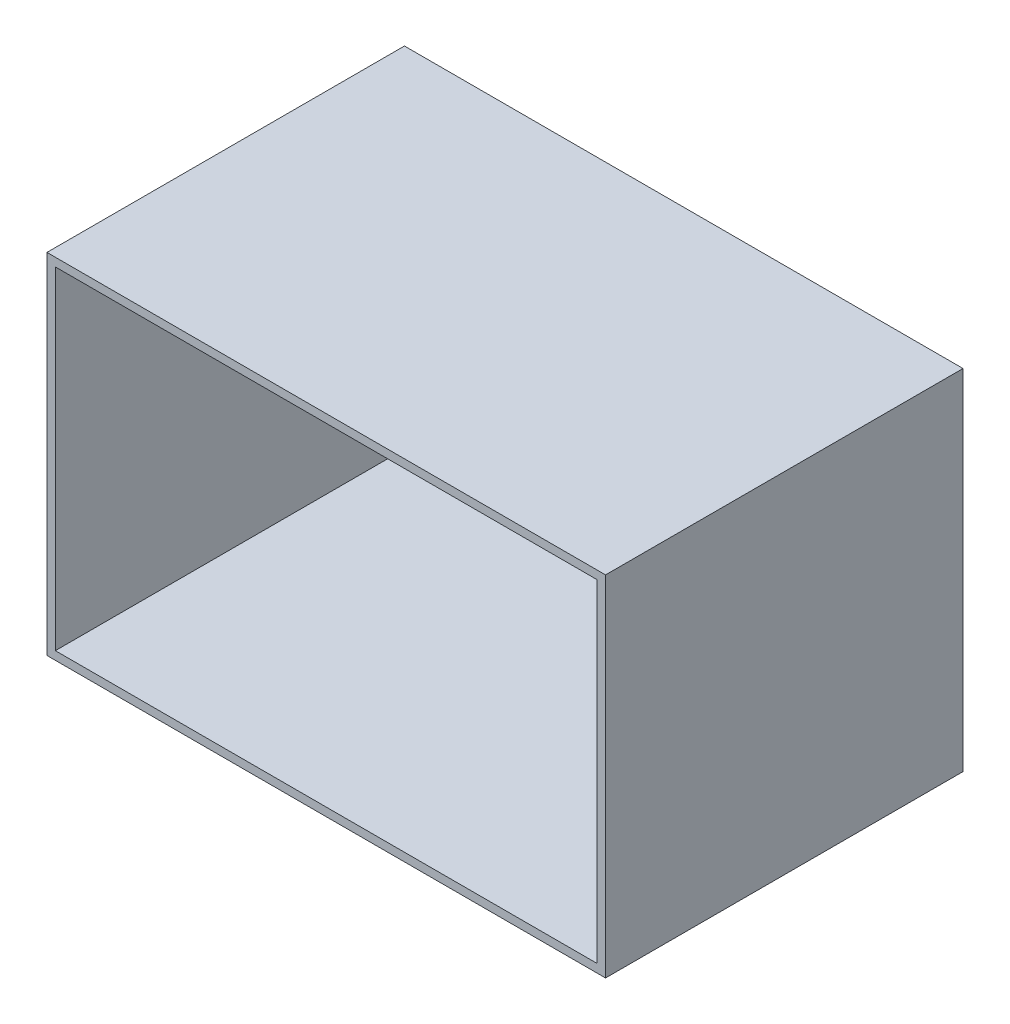
SolidWorks part; units mm, degrees
ref_plane "Alzado" through (0, 0, 0) normal (0, 0, 1) x (1, 0, 0)
ref_plane "Planta" through (0, 0, 0) normal (0, 1, 0) x (1, 0, 0)
ref_plane "Vista lateral" through (0, 0, 0) normal (1, 0, 0) x (0, 0, -1)
sketch "Croquis1" plane through (0, 0, 0) normal (0, 0, 1) x (1, 0, 0)
  line L1 (-200, 125) -> (200, 125)
  line L2 (-200, 125) -> (-200, -125)
  line L3 (-200, -125) -> (200, -125)
  line L4 (200, 125) -> (200, -125)
  line L5 (-200, 125) -> (200, -125) construction
  line L6 (-200, -125) -> (200, 125) construction
  point P0 (0, 0)
  dimension "D1" = 400
  dimension "D2" = 250
extrude "Saliente-Extruir2" add sketch "Croquis1" along normal blind 6
sketch "Croquis2" plane through (0, 0, 6) normal (0, 0, 1) x (1, 0, 0)
  line L1 (-194, 119) -> (194, 119)
  line L2 (-194, 119) -> (-194, -119)
  line L3 (-194, -119) -> (194, -119)
  line L4 (200, -125) -> (200, 125)
  line L5 (200, 125) -> (-200, 125)
  line L6 (-200, 125) -> (-200, -125)
  line L7 (-200, -125) -> (200, -125)
  line L8 (200, -125) -> (200, 125)
  line L9 (200, 125) -> (-200, 125)
  line L10 (-200, 125) -> (-200, -125)
  line L11 (-200, -125) -> (200, -125)
  line L12 (194, 119) -> (194, -119)
  line L13 (-194, 119) -> (194, -119) construction
  line L14 (-194, -119) -> (194, 119) construction
  point P2 (0, 0)
  dimension "D2" = 6
  dimension "D3" = 6
  dimension "D1" = 0
extrude "Saliente-Extruir3" add sketch "Croquis2" along normal blind 250
